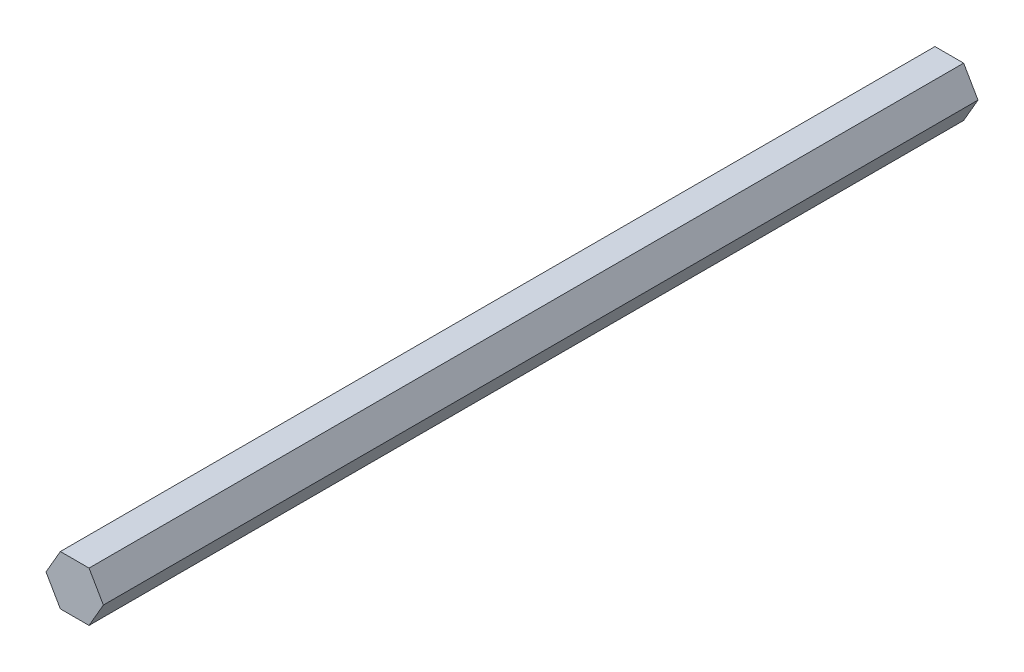
SolidWorks part; units mm, degrees
ref_plane "Front Plane" through (0, 0, 0) normal (0, 0, 1) x (1, 0, 0)
ref_plane "Top Plane" through (0, 0, 0) normal (0, 1, 0) x (1, 0, 0)
ref_plane "Right Plane" through (0, 0, 0) normal (1, 0, 0) x (0, 0, -1)
sketch "Sketch1" plane through (0, 0, 0) normal (0, 0, 1) x (1, 0, 0)
  line L1 (-7.3323, 0) -> (-3.6662, -6.35)
  line L2 (-3.6662, -6.35) -> (3.6662, -6.35)
  line L3 (3.6662, -6.35) -> (7.3323, 0)
  line L4 (7.3323, 0) -> (3.6662, 6.35)
  line L5 (3.6662, 6.35) -> (-3.6662, 6.35)
  line L6 (-3.6662, 6.35) -> (-7.3323, 0)
  circle A0 centre (0, 0) radius 6.35 construction
  dimension "D1" = 12.7
extrude "Boss-Extrude1" add sketch "Sketch1" along normal blind 223.52
